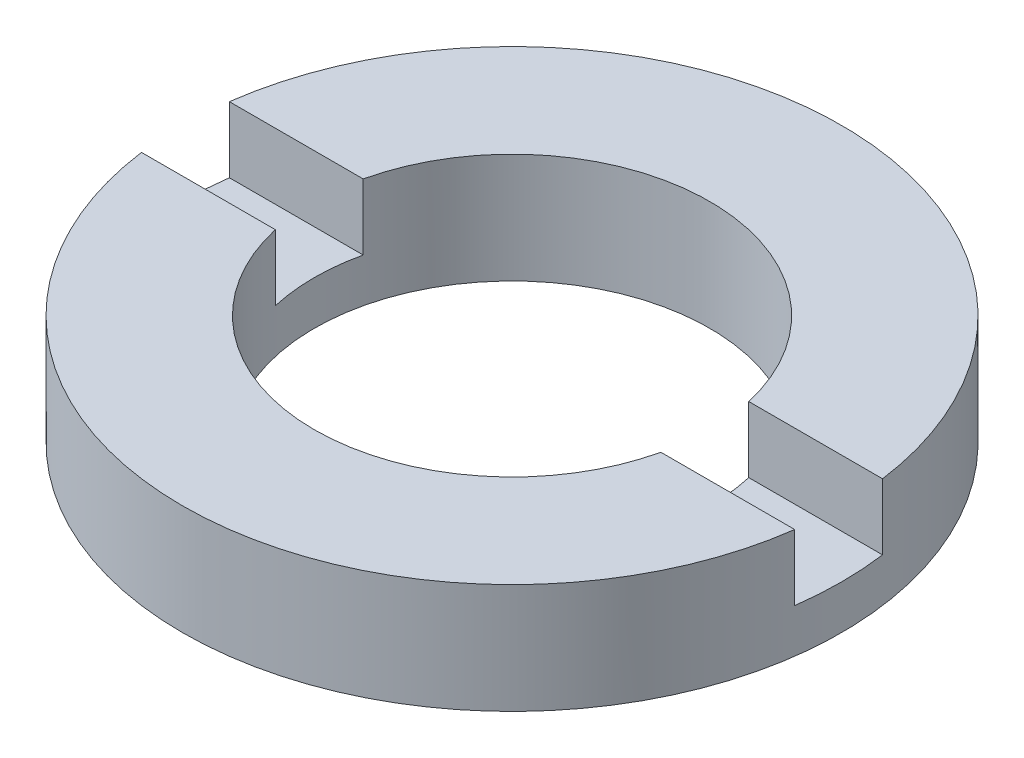
SolidWorks part; units mm, degrees
ref_plane "前视基准面" through (0, 0, 0) normal (0, 0, 1) x (1, 0, 0)
ref_plane "上视基准面" through (0, 0, 0) normal (0, 1, 0) x (1, 0, 0)
ref_plane "右视基准面" through (0, 0, 0) normal (1, 0, 0) x (0, 0, -1)
sketch "草图1" plane through (0, 0, 0) normal (0, 0, 1) x (1, 0, 0)
  line L0 (0, 56.2608) -> (0, -99.1922) construction
  line L1 (4.5, -1.9642) -> (7.5, -1.9642)
  line L4 (7.5, -1.9642) -> (7.5, -4.4642)
  line L5 (4.5, -4.4642) -> (4.5, -1.9642)
  line L7 (4.5, -4.4642) -> (7.5, -4.4642)
  dimension "D1" = 2.5
  dimension "D2" = 7.5
  dimension "D3" = 4.5
revolve "旋转1" add sketch "草图1" angle 360 about L0
cosmetic thread "装饰螺纹线1" parameters "D2"=14
sketch "草图2" plane through (0, -1.9642, 0) normal (0, 1, 0) x (1, 0, 0)
  line L0 (-28.67, 0) -> (29.9422, 0) construction
  line L2 (-26.8525, 1) -> (26.8525, 1)
  line L3 (-26.8525, 1) -> (-26.8525, -1)
  line L4 (-26.8525, -1) -> (26.8525, -1)
  line L5 (26.8525, 1) -> (26.8525, -1)
  line L6 (-26.8525, 1) -> (26.8525, -1) construction
  line L7 (-26.8525, -1) -> (26.8525, 1) construction
  point P3 (0, 0)
  dimension "D1" = 2
extrude "切除-拉伸1" cut sketch "草图2" against normal blind 1.5
